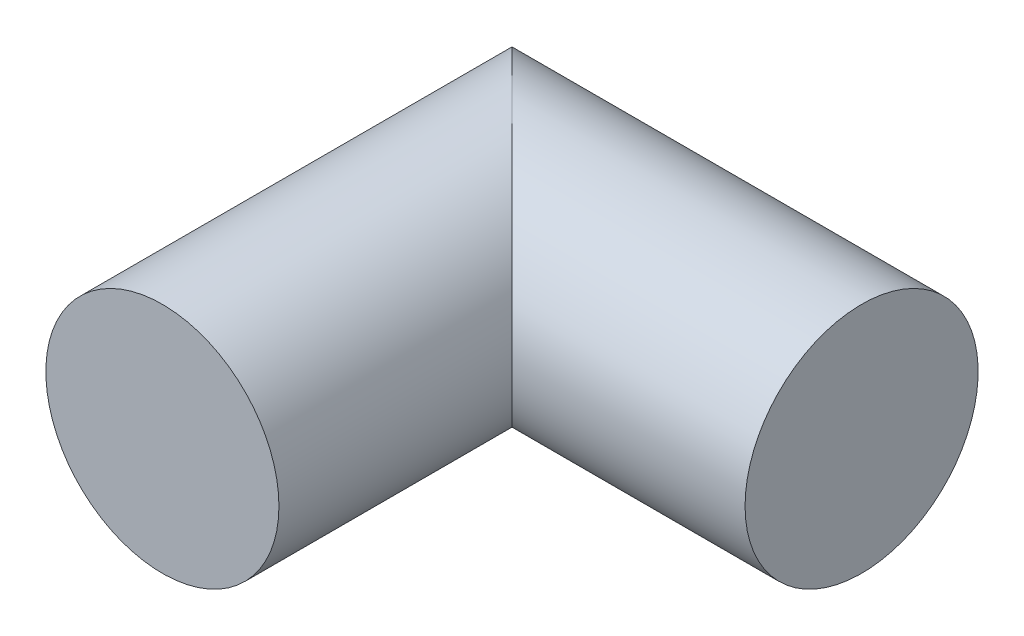
SolidWorks part; units mm, degrees
ref_plane "Front Plane" through (0, 0, 0) normal (0, 0, 1) x (1, 0, 0)
ref_plane "Top Plane" through (0, 0, 0) normal (0, 1, 0) x (1, 0, 0)
ref_plane "Right Plane" through (0, 0, 0) normal (1, 0, 0) x (0, 0, -1)
sketch3d "3DSketch2"
  line L0 (0, 0, 0) -> (-15, 0, 0)
  line L1 (-15, 0, 0) -> (-15, 0, 15)
  dimension "D1" = 15
  dimension "D2" = 15
ref_plane "Plane1" through (0, 0, 0) normal (-1, 0, 0) x (0, 0, 1)
sketch "Sketch3" plane through (0, 0, 0) normal (-1, 0, 0) x (0, 0, 1)
  circle A0 centre (0, 0) radius 5
  dimension "D1" = 10
sweep "Sweep1" add profiles "Sketch3" path "3DSketch2"
